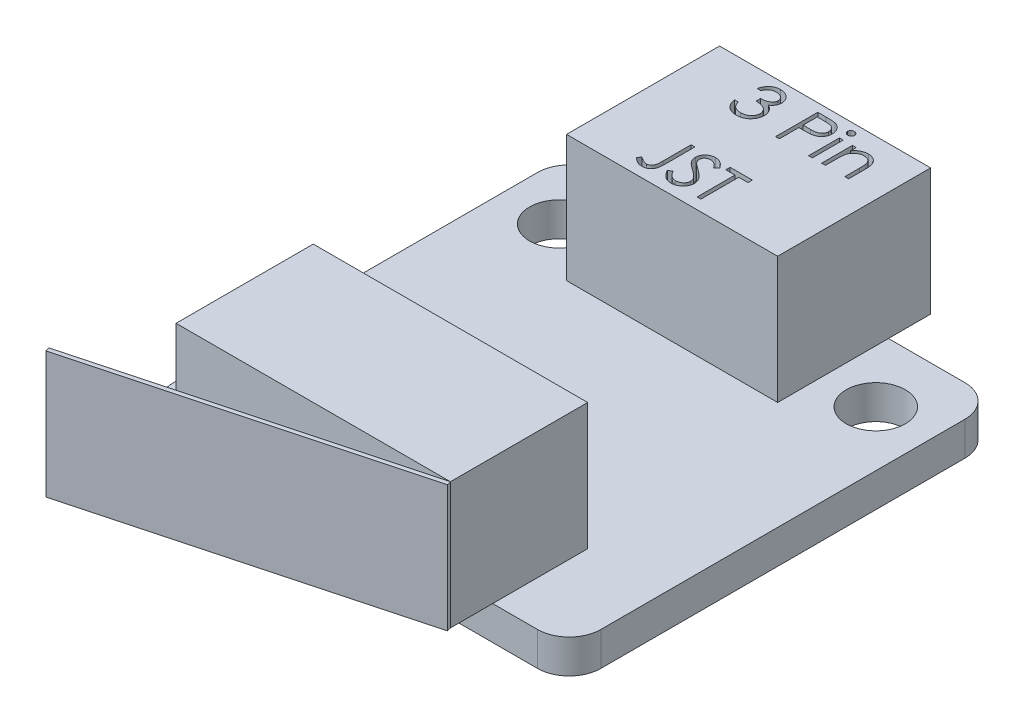
SolidWorks part; units mm, degrees
ref_plane "Front Plane" through (0, 0, 0) normal (0, 0, 1) x (1, 0, 0)
ref_plane "Top Plane" through (0, 0, 0) normal (0, 1, 0) x (1, 0, 0)
ref_plane "Right Plane" through (0, 0, 0) normal (1, 0, 0) x (0, 0, -1)
sketch "Sketch1" plane through (0, 0, 0) normal (0, 1, 0) x (1, 0, 0)
  line L0 (-7.5, 7.025) -> (7.5, 7.025) construction
  line L1 (-8.625, -10.125) -> (8.625, -10.125)
  line L2 (-10.125, -8.625) -> (-10.125, 8.625)
  line L3 (-8.625, 10.125) -> (8.625, 10.125)
  line L4 (10.125, -8.625) -> (10.125, 8.625)
  line L5 (-10.125, -10.125) -> (10.125, 10.125) construction
  line L6 (-10.125, 10.125) -> (10.125, -10.125) construction
  circle A0 centre (-7.5, 7.025) radius 1.4
  circle A1 centre (7.5, 7.025) radius 1.4
  arc A2 (-8.625, -10.125) -> (-10.125, -8.625) centre (-8.625, -8.625) cw
  arc A3 (8.625, -10.125) -> (10.125, -8.625) centre (8.625, -8.625) ccw
  arc A4 (8.625, 10.125) -> (10.125, 8.625) centre (8.625, 8.625) cw
  arc A5 (-10.125, 8.625) -> (-8.625, 10.125) centre (-8.625, 8.625) cw
  point P0 (0, 0)
  point P10 (0, 7.025)
extrude "Boss-Extrude1" add sketch "Sketch1" along normal blind 1.6
sketch "Sketch2" plane through (0, 1.6, 0) normal (0, 1, 0) x (1, 0, 0)
  line L0 (8.625, 10.125) -> (-8.625, 10.125) construction
  line L1 (-5, 4.875) -> (5, 4.875)
  line L2 (-5, 4.875) -> (-5, 12.125)
  line L3 (-5, 12.125) -> (5, 12.125)
  line L4 (5, 4.875) -> (5, 12.125)
  line L5 (-5, 4.875) -> (5, 12.125) construction
  line L6 (-5, 12.125) -> (5, 4.875) construction
  line L7 (-8.625, -10.125) -> (8.625, -10.125) construction
  line L8 (-6.5, -12.125) -> (6.5, -12.125)
  line L9 (-6.5, -12.125) -> (-6.5, -5.625)
  line L10 (-6.5, -5.625) -> (6.5, -5.625)
  line L11 (6.5, -12.125) -> (6.5, -5.625)
  line L12 (-6.5, -12.125) -> (6.5, -5.625) construction
  line L13 (-6.5, -5.625) -> (6.5, -12.125) construction
  line L14 (6.5, -12.125) -> (-8.5, -16.1442)
  line L15 (-8.5, -16.1442) -> (-8.4482, -16.3374)
  line L16 (-8.4482, -16.3374) -> (6.5518, -12.3182)
  line L17 (6.5518, -12.3182) -> (6.5, -12.125)
  point P0 (0, 8.5)
  point P9 (0, -8.875)
  line M10 (-8.625, -10.125) -> (8.625, -10.125)
  line M14 (8.625, 10.125) -> (-8.625, 10.125)
  dimension "D1" = 10
  dimension "D2" = 7.25
  dimension "D3" = 2
  dimension "D4" = 13
  dimension "D5" = 6.5
  dimension "D6" = 2
  dimension "D7" = 0.2
  dimension "D8" = 15
  dimension "D9" = 2
extrude "Boss-Extrude2" add sketch "Sketch2" along normal blind 6 contours L11 L10 L9 M10 | L4 L3 L2 M14 | L1 L4 L2 M14 | L8 L11 L9 M10 | L16 L17 L14 L15
sketch "Sketch3" plane through (0, 7.6, 0) normal (0, 1, 0) x (1, 0, 0)
  text T0 "3 Pin \r\nJST" font "Century Gothic" height 2
  point P1 (-2.3491, 9.2639)
  point P2 (-2.5199, 9.7337)
extrude "Cut-Extrude1" cut sketch "Sketch3" against normal blind 1
equation "\"D3@Sketch1\"=12.2+\"D2@Sketch1\""
